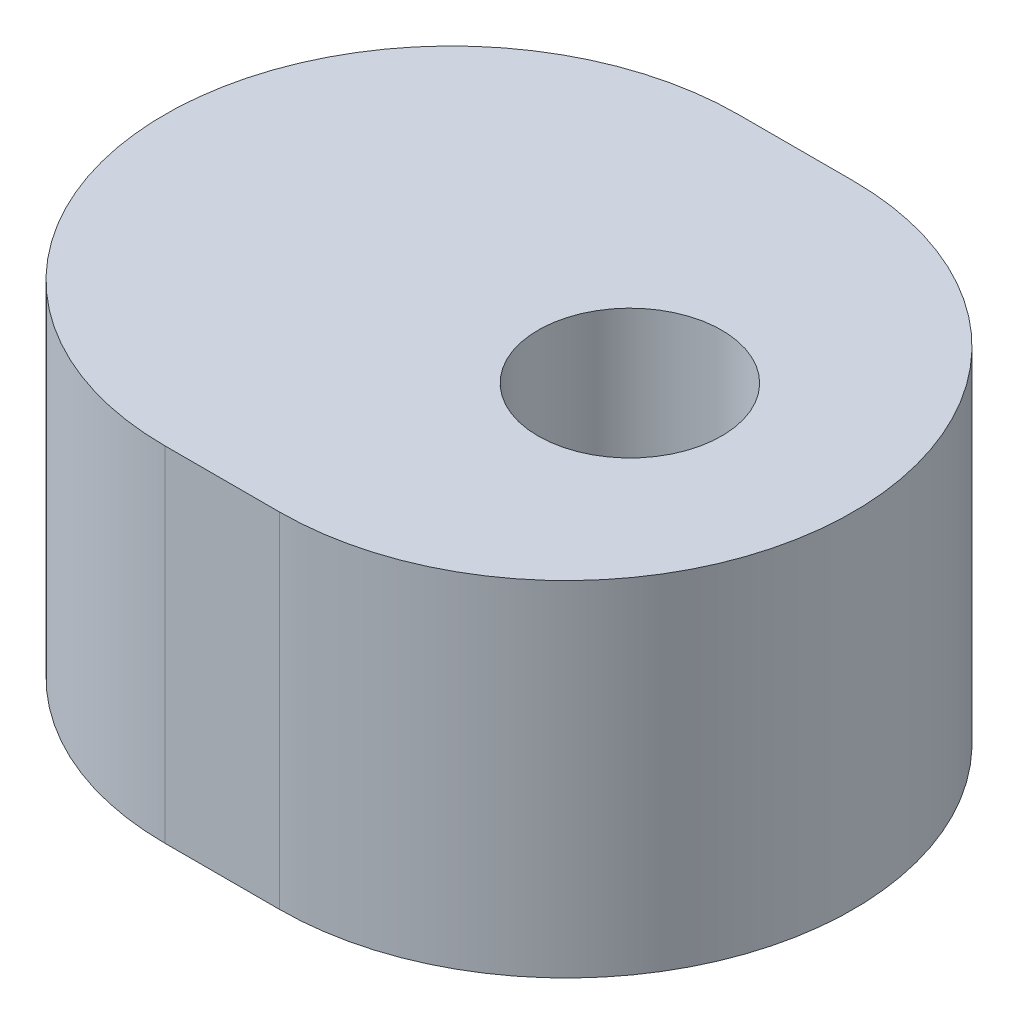
SolidWorks part; units mm, degrees
material "MDF"
ref_plane "Plano frontal" through (0, 0, 0) normal (0, 0, 1) x (1, 0, 0)
ref_plane "Plano superior" through (0, 0, 0) normal (0, 1, 0) x (1, 0, 0)
ref_plane "Plano direito" through (0, 0, 0) normal (1, 0, 0) x (0, 0, -1)
ref_plane "Plano1" through (0, -18, 0) normal (0, -1, 0) x (1, 0, 0)
sketch "Esboço1" plane through (0, -18, 0) normal (0, -1, 0) x (1, 0, 0)
  line L0 (-3.1073, -5) -> (-1.1073, -5)
  line L1 (-1.1073, 5) -> (-3.1073, 5)
  line L2 (-2.1073, 5) -> (-2.1073, -5) construction
  line L3 (-2.1073, 0) -> (0, 0) construction
  circle A0 centre (0, 0) radius 1.6
  arc A1 (-3.1073, 5) -> (-3.1073, -5) centre (-3.1073, 0) ccw
  arc A2 (-1.1073, -5) -> (-1.1073, 5) centre (-1.1073, 0) ccw
  dimension "D1" = 3.2
  dimension "D2" = 5
  dimension "D4" = 2
  dimension "D3" = 3.1073
extrude "Ressalto-extrusão1" add sketch "Esboço1" against normal blind 6
